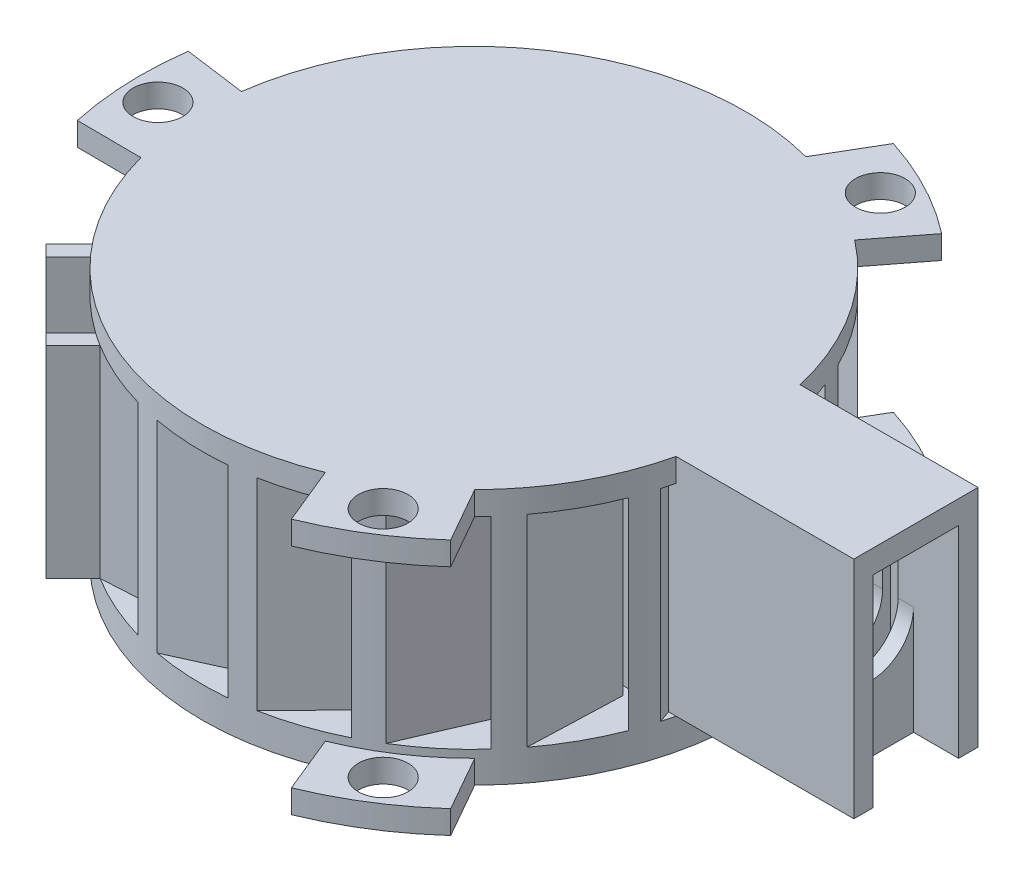
SolidWorks part; units mm, degrees
ref_plane "Front Plane" through (0, 0, 0) normal (0, 0, 1) x (1, 0, 0)
ref_plane "Top Plane" through (0, 0, 0) normal (0, 1, 0) x (1, 0, 0)
ref_plane "Right Plane" through (0, 0, 0) normal (1, 0, 0) x (0, 0, -1)
sketch "Sketch1" plane through (0, 0, 0) normal (0, 1, 0) x (1, 0, 0)
  circle A0 centre (0, 0) radius 17.5
  dimension "D1" = 35
extrude "Boss-Extrude1" add sketch "Sketch1" along normal blind 2
sketch "Sketch6" plane through (0, 2, 0) normal (0, 1, 0) x (1, 0, 0)
  line L1 (0, 17.5) -> (-4.9149, 14.0585)
  line L2 (-4.9149, 14.0585) -> (-4.3413, 13.2394)
  line L3 (-4.3413, 13.2394) -> (-1.7776, 15.0346)
  line L4 (-1.3536, 15.3315) -> (-0.3275, 12.5124) construction
  line L5 (-1.7776, 15.0346) -> (-0.5805, 11.7456)
  line L6 (-1.0084, 15.5731) -> (0.1886, 12.2842)
  line L7 (-0.5805, 11.7456) -> (0.1886, 12.2842)
  line L8 (-1.0084, 15.5731) -> (1.6342, 17.4235)
  line L9 (6.3217, 16.3183) -> (0.4955, 14.8847)
  line L10 (0.4955, 14.8847) -> (0.7344, 13.9136)
  line L11 (0.7344, 13.9136) -> (3.7736, 14.6614)
  line L12 (3.7736, 14.6614) -> (3.7017, 11.1622)
  line L13 (3.7017, 11.1622) -> (4.6135, 11.3865)
  line L14 (4.6853, 14.8858) -> (4.6135, 11.3865)
  line L15 (4.6853, 14.8858) -> (7.818, 15.6566)
  line L16 (11.7897, 12.9327) -> (5.839, 13.7005)
  line L17 (5.839, 13.7005) -> (5.711, 12.7088)
  line L18 (5.711, 12.7088) -> (8.8151, 12.3082)
  line L19 (8.8151, 12.3082) -> (7.484, 9.0712)
  line L20 (7.484, 9.0712) -> (8.4152, 8.951)
  line L21 (9.7463, 12.188) -> (8.4152, 8.951)
  line L22 (9.7463, 12.188) -> (12.9459, 11.7752)
  line L23 (15.6654, 7.8004) -> (10.3939, 10.6661)
  line L24 (10.3939, 10.6661) -> (9.9163, 9.7875)
  line L25 (9.9163, 9.7875) -> (12.666, 8.2927)
  line L26 (12.666, 8.2927) -> (10.2555, 5.7551)
  line L27 (10.2555, 5.7551) -> (11.0804, 5.3067)
  line L28 (13.491, 7.8442) -> (11.0804, 5.3067)
  line L29 (13.491, 7.8442) -> (16.3253, 6.3034)
  line L30 (17.4253, 1.6147) -> (13.5451, 6.1911)
  line L31 (13.5451, 6.1911) -> (12.7823, 5.5444)
  line L32 (12.7823, 5.5444) -> (14.8064, 3.1572)
  line L33 (14.8064, 3.1572) -> (11.642, 1.6618)
  line L34 (11.642, 1.6618) -> (12.2492, 0.9456)
  line L35 (15.4136, 2.441) -> (12.2492, 0.9456)
  line L36 (15.4136, 2.441) -> (17.5, -0.0196)
  line L37 (16.8319, -4.7891) -> (14.8669, 0.88)
  line L38 (14.8669, 0.88) -> (13.922, 0.5525)
  line L39 (13.922, 0.5525) -> (14.9471, -2.4047)
  line L40 (14.9471, -2.4047) -> (11.4561, -2.656)
  line L41 (11.4561, -2.656) -> (11.7636, -3.5432)
  line L42 (15.2546, -3.2919) -> (11.7636, -3.5432)
  line L43 (15.2546, -3.2919) -> (16.3112, -6.34)
  line L44 (13.9653, -10.5461) -> (14.1809, -4.55)
  line L45 (14.1809, -4.55) -> (13.1815, -4.5141)
  line L46 (13.1815, -4.5141) -> (13.0691, -7.6418)
  line L47 (13.0691, -7.6418) -> (9.723, -6.6151)
  line L48 (9.723, -6.6151) -> (9.6893, -7.5534)
  line L49 (13.0353, -8.5802) -> (9.6893, -7.5534)
  line L50 (13.0353, -8.5802) -> (12.9194, -11.8042)
  line L51 (9.2126, -14.8788) -> (11.5796, -9.3654)
  line L52 (11.5796, -9.3654) -> (10.6607, -8.9709)
  line L53 (10.6607, -8.9709) -> (9.426, -11.8469)
  line L54 (9.426, -11.8469) -> (6.6768, -9.6807)
  line L55 (6.6768, -9.6807) -> (6.3064, -10.5435)
  line L56 (9.0556, -12.7097) -> (6.3064, -10.5435)
  line L57 (9.0556, -12.7097) -> (7.7829, -15.6741)
  line L58 (3.2156, -17.202) -> (7.4145, -12.9161)
  line L59 (7.4145, -12.9161) -> (6.7001, -12.2162)
  line L60 (6.7001, -12.2162) -> (4.5099, -14.4519)
  line L61 (4.5099, -14.4519) -> (2.7289, -11.439)
  line L62 (2.7289, -11.439) -> (2.0718, -12.1097)
  line L63 (3.8528, -15.1227) -> (2.0718, -12.1097)
  line L64 (3.8528, -15.1227) -> (1.5952, -17.4271)
  line L65 (-3.2156, -17.202) -> (2.248, -14.7223)
  line L66 (2.248, -14.7223) -> (1.8347, -13.8117)
  line L67 (1.8347, -13.8117) -> (-1.0153, -15.1052)
  line L68 (-1.0153, -15.1052) -> (-1.5876, -11.6523)
  line L69 (-1.5876, -11.6523) -> (-2.4426, -12.0404)
  line L70 (-1.8703, -15.4933) -> (-2.4426, -12.0404)
  line L71 (-1.8703, -15.4933) -> (-4.808, -16.8266)
  line L72 (-9.2126, -14.8788) -> (-3.2221, -14.5402)
  line L73 (-3.2221, -14.5402) -> (-3.2786, -13.5418)
  line L74 (-3.2786, -13.5418) -> (-6.4033, -13.7184)
  line L75 (-6.4033, -13.7184) -> (-5.6897, -10.2919)
  line L76 (-5.6897, -10.2919) -> (-6.6272, -10.3449)
  line L77 (-7.3408, -13.7714) -> (-6.6272, -10.3449)
  line L78 (-7.3408, -13.7714) -> (-10.5618, -13.9535)
  line L79 (-13.9653, -10.5461) -> (-8.2571, -12.3943)
  line L80 (-8.2571, -12.3943) -> (-7.949, -11.443)
  line L81 (-7.949, -11.443) -> (-10.9266, -10.4789)
  line L82 (-10.9266, -10.4789) -> (-9.0234, -7.5416)
  line L83 (-9.0234, -7.5416) -> (-9.9167, -7.2523)
  line L84 (-11.8199, -10.1896) -> (-9.9167, -7.2523)
  line L85 (-11.8199, -10.1896) -> (-14.8891, -9.1959)
  line L86 (-16.8319, -4.7891) -> (-12.1768, -8.5746)
  line L87 (-12.1768, -8.5746) -> (-11.5459, -7.7987)
  line L88 (-11.5459, -7.7987) -> (-13.9742, -5.8241)
  line L89 (-13.9742, -5.8241) -> (-11.1384, -3.7727)
  line L90 (-11.1384, -3.7727) -> (-11.8669, -3.1803)
  line L91 (-14.7027, -5.2317) -> (-11.8669, -3.1803)
  line L92 (-14.7027, -5.2317) -> (-17.2056, -3.1963)
  line L93 (-17.4253, 1.6147) -> (-14.4521, -3.5968)
  line L94 (-14.4521, -3.5968) -> (-13.5835, -3.1012)
  line L95 (-13.5835, -3.1012) -> (-15.1344, -0.3828)
  line L96 (-15.1344, -0.3828) -> (-11.7491, 0.5057)
  line L97 (-11.7491, 0.5057) -> (-12.2144, 1.3213)
  line L98 (-15.5997, 0.4328) -> (-12.2144, 1.3213)
  line L99 (-15.5997, 0.4328) -> (-17.1984, 3.2349)
  line L100 (-15.6654, 7.8004) -> (-14.7755, 1.8668)
  line L101 (-14.7755, 1.8668) -> (-13.7865, 2.0151)
  line L102 (-13.7865, 2.0151) -> (-14.2507, 5.1103)
  line L103 (-14.2507, 5.1103) -> (-10.773, 4.7158)
  line L104 (-10.773, 4.7158) -> (-10.9123, 5.6444)
  line L105 (-14.39, 6.0388) -> (-10.9123, 5.6444)
  line L106 (-14.39, 6.0388) -> (-14.8685, 9.2292)
  line L107 (-11.7897, 12.9327) -> (-13.1033, 7.0782)
  line L108 (-13.1033, 7.0782) -> (-12.1276, 6.8593)
  line L109 (-12.1276, 6.8593) -> (-11.4424, 9.9131)
  line L110 (-11.4424, 9.9131) -> (-8.342, 8.289)
  line L111 (-8.342, 8.289) -> (-8.1364, 9.2052)
  line L112 (-11.2368, 10.8293) -> (-8.1364, 9.2052)
  line L113 (-11.2368, 10.8293) -> (-10.5304, 13.9771)
  line L114 (-6.3217, 16.3183) -> (-9.6616, 11.3337)
  line L115 (-9.6616, 11.3337) -> (-8.8308, 10.7771)
  line L116 (-8.8308, 10.7771) -> (-7.0886, 13.3772)
  line L117 (-7.0886, 13.3772) -> (-4.7843, 10.7428)
  line L118 (-4.7843, 10.7428) -> (-4.2617, 11.5228)
  line L119 (-6.566, 14.1572) -> (-4.2617, 11.5228)
  line L120 (-6.566, 14.1572) -> (-4.7702, 16.8373)
  circle A1 centre (0, 0) radius 17.5
  arc A2 (1.6342, 17.4235) -> (0, 17.5) centre (0, 0) ccw
  arc A3 (7.818, 15.6566) -> (6.3217, 16.3183) centre (0, 0) ccw
  arc A4 (12.9459, 11.7752) -> (11.7897, 12.9327) centre (0, 0) ccw
  arc A5 (16.3253, 6.3034) -> (15.6654, 7.8004) centre (0, 0) ccw
  arc A6 (17.5, -0.0196) -> (17.4253, 1.6147) centre (0, 0) ccw
  arc A7 (16.3112, -6.34) -> (16.8319, -4.7891) centre (0, 0) ccw
  arc A8 (12.9194, -11.8042) -> (13.9653, -10.5461) centre (0, 0) ccw
  arc A9 (7.7829, -15.6741) -> (9.2126, -14.8788) centre (0, 0) ccw
  arc A10 (1.5952, -17.4271) -> (3.2156, -17.202) centre (0, 0) ccw
  arc A11 (-4.808, -16.8266) -> (-3.2156, -17.202) centre (0, 0) ccw
  arc A12 (-10.5618, -13.9535) -> (-9.2126, -14.8788) centre (0, 0) ccw
  arc A13 (-14.8891, -9.1959) -> (-13.9653, -10.5461) centre (0, 0) ccw
  arc A14 (-17.2056, -3.1963) -> (-16.8319, -4.7891) centre (0, 0) ccw
  arc A15 (-17.1984, 3.2349) -> (-17.4253, 1.6147) centre (0, 0) ccw
  arc A16 (-14.8685, 9.2292) -> (-15.6654, 7.8004) centre (0, 0) ccw
  arc A17 (-10.5304, 13.9771) -> (-11.7897, 12.9327) centre (0, 0) ccw
  arc A18 (-4.7702, 16.8373) -> (-6.3217, 16.3183) centre (0, 0) ccw
  point P135 (0, 0)
  point P143 (0, 0)
  dimension "D2" = 6
  dimension "D3" = 3.5
  dimension "D4" = 1
  dimension "D5" = 3
  dimension "D6" = 75
  dimension "D7" = 0.5
  dimension "D8" = 3.5
  dimension "D9" = 17
  dimension "D1" = 0
extrude "Boss-Extrude2" add sketch "Sketch6" along normal blind 13
sketch "Sketch7" plane through (0, 2, 0) normal (0, 1, 0) x (1, 0, 0)
  line L0 (0, 0) -> (28.1783, 0) construction
  line L1 (11.5, 4) -> (28.5, 4)
  line L2 (11.5, 4) -> (11.5, -4)
  line L3 (11.5, -4) -> (28.5, -4)
  line L4 (28.5, 4) -> (28.5, -4)
  line L5 (17.5, 0) -> (17.5, -7.7892) construction
  arc A0 (17.5, -0.0196) -> (17.4253, 1.6147) centre (0, 0) ccw construction
  arc A3 (17.5, -0.0196) -> (17.5, 0) centre (0, 0) ccw
  dimension "D1" = 8
  dimension "D2" = 17
  dimension "D3" = 4
  dimension "D4" = 6
extrude "Boss-Extrude3" add sketch "Sketch7" along normal blind 13
sketch "Sketch8" plane through (0, 15, 0) normal (0, 1, 0) x (1, 0, 0)
  line L0 (11.5, 4) -> (11.5, -4) construction
  line L1 (12.5, 2.75) -> (27.5, 2.75)
  line L2 (12.5, 2.75) -> (12.5, -2.75)
  line L3 (12.5, -2.75) -> (27.5, -2.75)
  line L4 (27.5, 2.75) -> (27.5, -2.75)
  line L5 (0, 0) -> (29.6487, 0) construction
  dimension "D1" = 5.5
  dimension "D2" = 1
  dimension "D3" = 2.75
  dimension "D4" = 15
extrude "Cut-Extrude1" cut sketch "Sketch8" against normal blind 6
sketch "Sketch10" plane through (0, 9, 0) normal (0, 1, 0) x (1, 0, 0)
  line L0 (12.5, -2.75) -> (27.5, -2.75) construction
  line L1 (12.5, 2.75) -> (16, 2.75)
  line L2 (12.5, 2.75) -> (12.5, -2.75)
  line L3 (12.5, -2.75) -> (16, -2.75)
  line L4 (16, 2.75) -> (16, -2.75)
  dimension "D1" = 3.5
extrude "Cut-Extrude2" cut sketch "Sketch10" against normal blind 6
sketch "Sketch14" plane through (28.5, 0, 0) normal (1, 0, 0) x (0, 0, -1)
  line L0 (-2.75, 9) -> (2.75, 9) construction
  line L1 (4, 15) -> (-4, 15) construction
  line L2 (4, 15) -> (4, 2) construction
  line L3 (4, 2) -> (-4, 2) construction
  line L4 (-4, 15) -> (-4, 2) construction
  circle A0 centre (0, 9) radius 2.75
  dimension "D1" = 5.5
extrude "Cut-Extrude3" cut sketch "Sketch14" against normal blind 13 from surface at -1 contours A0 starting at face at (27.5, 12, 0)
sketch "Sketch15" plane through (0, 15, 0) normal (0, 1, 0) x (1, 0, 0)
  line L0 (12.5, -2.75) -> (27.5, -2.75) construction
  line L1 (27.5, 2.75) -> (25.5944, 2.75)
  line L2 (27.5, 2.75) -> (27.5, -2.75)
  line L3 (27.5, -2.75) -> (25.5944, -2.75)
  line L4 (25.5944, 2.75) -> (25.5944, -2.75)
  line L5 (27.5, 0) -> (24.81, 0) construction
  line L6 (25.5944, 1) -> (27.5, 1)
  line L7 (25.5944, 1) -> (25.5944, -1)
  line L8 (25.5944, -1) -> (27.5, -1)
  line L9 (27.5, 1) -> (27.5, -1)
  line M11 (12.5, 2.75) -> (27.5, 2.75)
  line M12 (27.5, 2.75) -> (27.5, -2.75)
  line M13 (27.5, -2.75) -> (12.5, -2.75)
  dimension "D1" = 1
  dimension "D2" = 1
extrude "Cut-Extrude4" cut sketch "Sketch15" against normal blind 13 contours L8 L4 M13 M12 | L4 L6 M12 M11
sketch "Sketch16" plane through (0, 15, 0) normal (0, 1, 0) x (1, 0, 0)
  line L0 (28.5, 4) -> (28.5, -4) construction
  line L1 (25.5944, 2.75) -> (28.5, 2.75)
  line L2 (25.5944, 2.75) -> (25.5944, -2.753)
  line L3 (25.5944, -2.753) -> (28.5, -2.753)
  line L4 (28.5, 2.75) -> (28.5, -2.753)
extrude "Cut-Extrude5" cut sketch "Sketch16" against normal blind 13
sketch "Sketch17" plane through (0, 15, 0) normal (0, 1, 0) x (1, 0, 0)
  line L0 (12.5, -2.75) -> (25.5944, -2.75) construction
  line L1 (16, 2.75) -> (23.6, 2.75)
  line L2 (16, 2.75) -> (16, -2.75)
  line L3 (16, -2.75) -> (23.6, -2.75)
  line L4 (23.6, 2.75) -> (23.6, -2.75)
  line L5 (23.6, 2.75) -> (24.2817, 2.75) construction
  line L6 (23.6, 3.25) -> (24.6, 3.25)
  line L7 (23.6, 3.25) -> (23.6, -3.25)
  line L8 (23.6, -3.25) -> (24.6, -3.25)
  line L9 (24.6, 3.25) -> (24.6, -3.25)
  line L10 (28.5, 2.75) -> (12.5, 2.75) construction
  line L11 (23.6, -2.75) -> (24.253, -2.75) construction
  line M11 (12.5, 2.75) -> (28.5, 2.75)
  line M30 (25.5944, -2.75) -> (12.5, -2.75)
  dimension "D1" = 7.6
  dimension "D2" = 0.5
  dimension "D3" = 6.5
  dimension "D4" = 1
extrude "Cut-Extrude6" cut sketch "Sketch17" against normal blind 10 contours L9 L6 L7 M11 | L9 L4 M11 M30 | L9 L7 L8 M30
sketch "Sketch18" plane through (12.5, 0, 0) normal (1, 0, 0) x (0, 0, -1)
  line L4 (2.75, 15) -> (-2.75, 15)
  line L5 (-2.75, 15) -> (-2.75, 3)
  line L6 (-2.75, 3) -> (2.75, 3)
  line L7 (2.75, 3) -> (2.75, 15)
  line L9 (-2.75, 15) -> (-2.75, 3)
  line L10 (-2.75, 3) -> (2.75, 3)
  line L11 (2.75, 3) -> (2.75, 15)
  line L13 (2.75, 15) -> (-2.75, 15)
  arc A0 (-2.75, 9) -> (2.75, 9) centre (0, 9) ccw construction
  arc A1 (-2.75, 9) -> (2.75, 9) centre (0, 9) ccw
  circle A2 centre (0, 9) radius 2
  dimension "D2" = 4
  dimension "D1" = 0
extrude "Cut-Extrude7" cut sketch "Sketch18" against normal blind 10 contours A2
sketch "Sketch20" plane through (0, 2, 0) normal (0, 1, 0) x (1, 0, 0)
  line L0 (16, 0) -> (-26.5681, 0) construction
  line L1 (16, 2.75) -> (16, -2.75) construction
  line L2 (0, 0) -> (-20.494, 20.494) construction
  line L3 (-28.2695, 3.5207) -> (-1.2716, -23.4772) construction
  line L4 (0, 0) -> (-20.8502, -20.8502) construction
  line L5 (-22.981, -17.3241) -> (-10.9602, -5.3033)
  line L6 (-5.3033, -10.9602) -> (-17.3241, -22.981)
  line L7 (-17.3241, -22.981) -> (-22.981, -17.3241)
  line L8 (-10.9602, -5.3033) -> (-5.3033, -10.9602)
  arc A0 (-16.8319, -4.7891) -> (-14.8891, -9.1959) centre (0, 0) ccw construction
  dimension "D1" = 135
  dimension "D2" = 4
  dimension "D3" = 4
  dimension "D4" = 6
  dimension "D5" = 17
extrude "Boss-Extrude4" add sketch "Sketch20" along normal blind 13
sketch "Sketch21" plane through (0, 15, 0) normal (0, 1, 0) x (1, 0, 0)
  line L0 (-10.9602, -6.7175) -> (-21.5668, -17.3241)
  line L1 (-21.5668, -17.3241) -> (-17.3241, -21.5668)
  line L2 (-17.3241, -21.5668) -> (-6.7175, -10.9602)
  line L3 (-6.7175, -10.9602) -> (-10.9602, -6.7175)
  line L4 (-5.9564, -10.307) -> (-10.9602, -5.3033) construction
  line L5 (-22.981, -17.3241) -> (-17.3241, -22.981) construction
  line L6 (-17.3241, -22.981) -> (-9.2184, -14.8752) construction
  line L7 (-14.8752, -9.2184) -> (-22.981, -17.3241) construction
  line L8 (-5.9564, -10.307) -> (-10.9602, -5.3033)
  line L9 (-22.981, -17.3241) -> (-17.3241, -22.981)
  line L10 (-17.3241, -22.981) -> (-9.2184, -14.8752)
  line L11 (-14.8752, -9.2184) -> (-22.981, -17.3241)
  dimension "D1" = 1
  dimension "D2" = 1
  dimension "D3" = 1
  dimension "D4" = 1
extrude "Cut-Extrude8" cut sketch "Sketch21" against normal blind 6 contours L2 L3 L0 L1
sketch "Sketch22" plane through (0, 9, 0) normal (0, 1, 0) x (1, 0, 0)
  line L0 (-10.9602, -6.7175) -> (-6.7175, -10.9602)
  line L1 (-6.7175, -10.9602) -> (-9.5459, -13.7886)
  line L2 (-17.3241, -21.5668) -> (-6.7175, -10.9602) construction
  line L3 (-9.5459, -13.7886) -> (-13.7886, -9.5459)
  line L4 (-10.9602, -6.7175) -> (-21.5668, -17.3241) construction
  line L5 (-13.7886, -9.5459) -> (-10.9602, -6.7175)
  dimension "D1" = 4
extrude "Cut-Extrude9" cut sketch "Sketch22" against normal blind 7
sketch "Sketch23" plane through (-11.6673, 0, 11.6673) normal (0.7071, 0, -0.7071) x (-0.7071, 0, -0.7071)
  line L0 (3, 9) -> (-3, 9) construction
  circle A0 centre (0, 9) radius 2.6
  dimension "D1" = 5.2
extrude "Cut-Extrude10" cut sketch "Sketch23" against normal blind 3
sketch "Sketch24" plane through (0, 15, 0) normal (0, 1, 0) x (1, 0, 0)
  line L0 (-22.981, -17.3241) -> (-16.617, -10.9602)
  line L1 (-14.8752, -9.2184) -> (-22.981, -17.3241) construction
  line L2 (-16.617, -10.9602) -> (-10.9602, -16.617)
  line L3 (-17.3241, -22.981) -> (-9.2184, -14.8752) construction
  line L4 (-10.9602, -16.617) -> (-17.3241, -22.981)
  line L5 (-17.3241, -22.981) -> (-22.981, -17.3241)
  line L6 (-15.6271, -11.9501) -> (-11.9501, -15.6271) construction
  dimension "D1" = 0
extrude "Cut-Extrude11" cut sketch "Sketch24" against normal blind 22
sketch "Sketch25" plane through (-13.7886, 0, 13.7886) normal (-0.7071, 0, 0.7071) x (0.7071, 0, 0.7071)
  arc A0 (-2.6, 9) -> (2.6, 9) centre (0, 9) ccw construction
  arc A1 (-2.6, 9) -> (2.6, 9) centre (0, 9) ccw
  circle A2 centre (0, 9) radius 2.6
  arc M6 (2.6, 9) -> (-2.6, 9) centre (0, 9) cw
extrude "Cut-Extrude12" cut sketch "Sketch25" against normal blind 17 contours A2 M6
sketch "Sketch26" plane through (0, 2, 0) normal (0, 1, 0) x (1, 0, 0)
  line L0 (-8.8388, -8.8388) -> (-13.7886, -13.7886) construction
  line L1 (-6.7175, -10.9602) -> (-10.9602, -6.7175) construction
  line L2 (-15.6271, -11.9501) -> (-11.9501, -15.6271) construction
  line L3 (-8.1317, -12.3744) -> (-12.3744, -8.1317) construction
  line L4 (-9.5459, -13.7886) -> (-6.7175, -10.9602) construction
  line L5 (-10.9602, -6.7175) -> (-13.7886, -9.5459) construction
sketch "Sketch27" plane through (0, 15, 0) normal (0, 1, 0) x (1, 0, 0)
  line L0 (-11.3137, -9.1924) -> (-10.9602, -8.8388)
  line L1 (-8.1317, -12.3744) -> (-12.3744, -8.1317) construction
  line L2 (-10.9602, -8.8388) -> (-8.8388, -10.9602)
  line L3 (-8.8388, -10.9602) -> (-9.5459, -11.6673)
  line L4 (-9.5459, -11.6673) -> (-11.6673, -9.5459)
  line L5 (-11.6673, -9.5459) -> (-11.3137, -9.1924)
  line L6 (-11.2189, -11.2189) -> (-9.4086, -9.4086) construction
  line L7 (-8.8388, -8.8388) -> (-13.7886, -13.7886) construction
  line L8 (-11.5867, -8.9194) -> (-8.7609, -11.7452) construction
  dimension "D1" = 3
  dimension "D2" = 0.5
  dimension "D3" = 0.5
  dimension "D4" = 1.5
extrude "Cut-Extrude15" cut sketch "Sketch27" against normal blind 22
sketch "Sketch28" plane through (0, 2, 0) normal (0, 1, 0) x (1, 0, 0)
  line L0 (-17.5, 0) -> (0, 0) construction
  line L1 (-13.7886, -13.7886) -> (-2.8382, -2.8382) construction
  line L2 (-1.9117, -3.145) -> (1.4471, -6.5038)
  line L3 (1.4471, -6.5038) -> (2.1542, -5.7966)
  line L7 (2.1542, -4.3824) -> (4.2755, -6.5038)
  line L8 (4.2755, -6.5038) -> (3.5684, -7.2109)
  line L9 (3.5684, -7.2109) -> (2.1542, -5.7966)
  line L10 (1.1542, -4.3824) -> (1.1542, -4.7966)
  line L12 (2.1542, -4.3824) -> (2.1542, -0.7233)
  line L14 (1.1542, -4.3824) -> (1.1542, -0.7233)
  line L15 (1.1542, -4.7966) -> (-1.2046, -2.4379)
  line L16 (1.1542, -0.7233) -> (2.1542, -0.7233)
  line L17 (2.162, 0) -> (47.4582, 0) construction
  line L18 (-1.9117, -3.145) -> (-1.2046, -2.4379)
  line L19 (-2.0807, -2.0807) -> (20.2405, 20.2405) construction
  arc A1 (-17.4253, 1.6147) -> (-17.2056, -3.1963) centre (0, 0) ccw construction
  dimension "D4" = 3
  dimension "D5" = 1
  dimension "D6" = 1
extrude "Boss-Extrude5" add sketch "Sketch28" along normal blind 13
sketch "Sketch29" plane through (0, 15, 0) normal (0, 1, 0) x (1, 0, 0)
  line L0 (-5.9564, -10.307) -> (-5.7383, -10.5252)
  line L1 (-5.9564, -10.307) -> (-5.6897, -10.2919)
  line L2 (-5.6897, -10.2919) -> (-5.7383, -10.5252)
extrude "Cut-Extrude16" cut sketch "Sketch29" against normal blind 13
sketch "Sketch30" plane through (0, 0, 0) normal (0, 1, 0) x (1, 0, 0)
  line L0 (8.8979, 14.5479) -> (11.8462, 18.8525) construction
  line L1 (9.2582, 20.7368) -> (5.9714, 15.9379) construction
  line L2 (4.4896, 16.9143) -> (6.5761, 20.4696)
  line L3 (10.7134, 13.8373) -> (13.1622, 17.0002)
  line L4 (12.4034, -12.3453) -> (14.4391, -15.9299)
  line L5 (6.6268, -16.1968) -> (8.1415, -19.8989)
  line L6 (-16.893, -4.569) -> (-21.0153, -4.5397)
  line L7 (-17.3402, 2.3594) -> (-21.3037, 2.8987)
  arc A0 (-21.3037, 2.8987) -> (-21.0153, -4.5397) centre (0, 0) ccw
  circle A1 centre (10.6021, -16.3958) radius 1.6
  arc A2 (-17.3402, 2.3594) -> (-16.893, -4.569) centre (0, 0) ccw
  circle A3 centre (8.8981, 17.3796) radius 1.6
  circle A4 centre (-19.5003, -0.9838) radius 1.6
  arc A5 (13.1622, 17.0002) -> (6.5761, 20.4696) centre (0, 0) ccw
  arc A6 (8.1415, -19.8989) -> (14.4391, -15.9299) centre (0, 0) ccw
  arc A7 (10.7134, 13.8373) -> (4.4896, 16.9143) centre (0, 0) ccw
  arc A8 (6.6268, -16.1968) -> (12.4034, -12.3453) centre (0, 0) ccw
  point P12 (0, 0)
  point P30 (0, 0)
  dimension "D1" = 43
  dimension "D2" = 35
  dimension "D3" = 3.2
  dimension "D5" = 3
  dimension "D4" = 3
extrude "Boss-Extrude6" add sketch "Sketch30" along normal blind 1.5 contours L4 A6 L5 A8 | L7 A0 L6 A2 | L2 A5 L3 A7
sketch "Sketch31" plane through (0, 2, 0) normal (0, 1, 0) x (1, 0, 0)
  circle A0 centre (8.9098, 17.2938) radius 1.6
  circle A1 centre (10.522, -16.363) radius 1.6
  circle A2 centre (-19.4318, -0.9308) radius 1.6
  point P8 (0, 0)
  dimension "D1" = 3.2
  dimension "D2" = 3
extrude "Cut-Extrude17" cut sketch "Sketch31" against normal blind 16.5
ref_plane "Plane1" through (0, 15, 0) normal (0, 1, 0) x (1, 0, 0)
sketch "Sketch32" plane through (0, 15, 0) normal (0, 1, 0) x (1, 0, 0)
  line L0 (6.6268, -16.1968) -> (8.1415, -19.8989) construction
  line L1 (14.4391, -15.9299) -> (12.4034, -12.3453) construction
  line L2 (10.7134, 13.8373) -> (13.1622, 17.0002) construction
  line L3 (6.5761, 20.4696) -> (4.4896, 16.9143) construction
  line L4 (-17.3402, 2.3594) -> (-21.3037, 2.8987) construction
  line L5 (-21.0153, -4.5397) -> (-16.893, -4.569) construction
  line L6 (6.6268, -16.1968) -> (8.1415, -19.8989)
  line L7 (14.4391, -15.9299) -> (12.4034, -12.3453)
  line L8 (10.7134, 13.8373) -> (13.1622, 17.0002)
  line L9 (6.5761, 20.4696) -> (4.4896, 16.9143)
  line L10 (-17.3402, 2.3594) -> (-21.3037, 2.8987)
  line L11 (-21.0153, -4.5397) -> (-16.893, -4.569)
  line L12 (17.0367, 4) -> (28.5, 4)
  line L13 (28.5, 4) -> (28.5, -4)
  line L14 (28.5, -4) -> (17.0367, -4)
  arc A0 (6.6268, -16.1968) -> (12.4034, -12.3453) centre (0, 0) ccw construction
  arc A1 (8.1415, -19.8989) -> (14.4391, -15.9299) centre (0, 0) ccw construction
  arc A2 (10.7134, 13.8373) -> (4.4896, 16.9143) centre (0, 0) ccw construction
  arc A3 (13.1622, 17.0002) -> (6.5761, 20.4696) centre (0, 0) ccw construction
  arc A4 (-17.3402, 2.3594) -> (-16.893, -4.569) centre (0, 0) ccw construction
  arc A5 (-21.3037, 2.8987) -> (-21.0153, -4.5397) centre (0, 0) ccw construction
  arc A6 (6.6268, -16.1968) -> (12.4034, -12.3453) centre (0, 0) ccw
  arc A7 (8.1415, -19.8989) -> (14.4391, -15.9299) centre (0, 0) ccw
  arc A8 (10.7134, 13.8373) -> (4.4896, 16.9143) centre (0, 0) ccw
  arc A9 (13.1622, 17.0002) -> (6.5761, 20.4696) centre (0, 0) ccw
  arc A10 (-17.3402, 2.3594) -> (-16.893, -4.569) centre (0, 0) ccw
  arc A11 (-21.3037, 2.8987) -> (-21.0153, -4.5397) centre (0, 0) ccw
  arc A12 (17.0367, 4) -> (17.0367, -4) centre (0, 0) ccw
  circle A13 centre (-19.4318, -0.9308) radius 1.6
  circle A14 centre (8.9098, 17.2938) radius 1.6
  circle A15 centre (10.522, -16.363) radius 1.6
extrude "Boss-Extrude7" add sketch "Sketch32" along normal blind 1.5 contours L10 A11 L11 A10 A13 | A6 A12 L14 L13 L12 A8 A10 | L8 A9 L9 A8 A14 | L6 A7 L7 A6 A15
